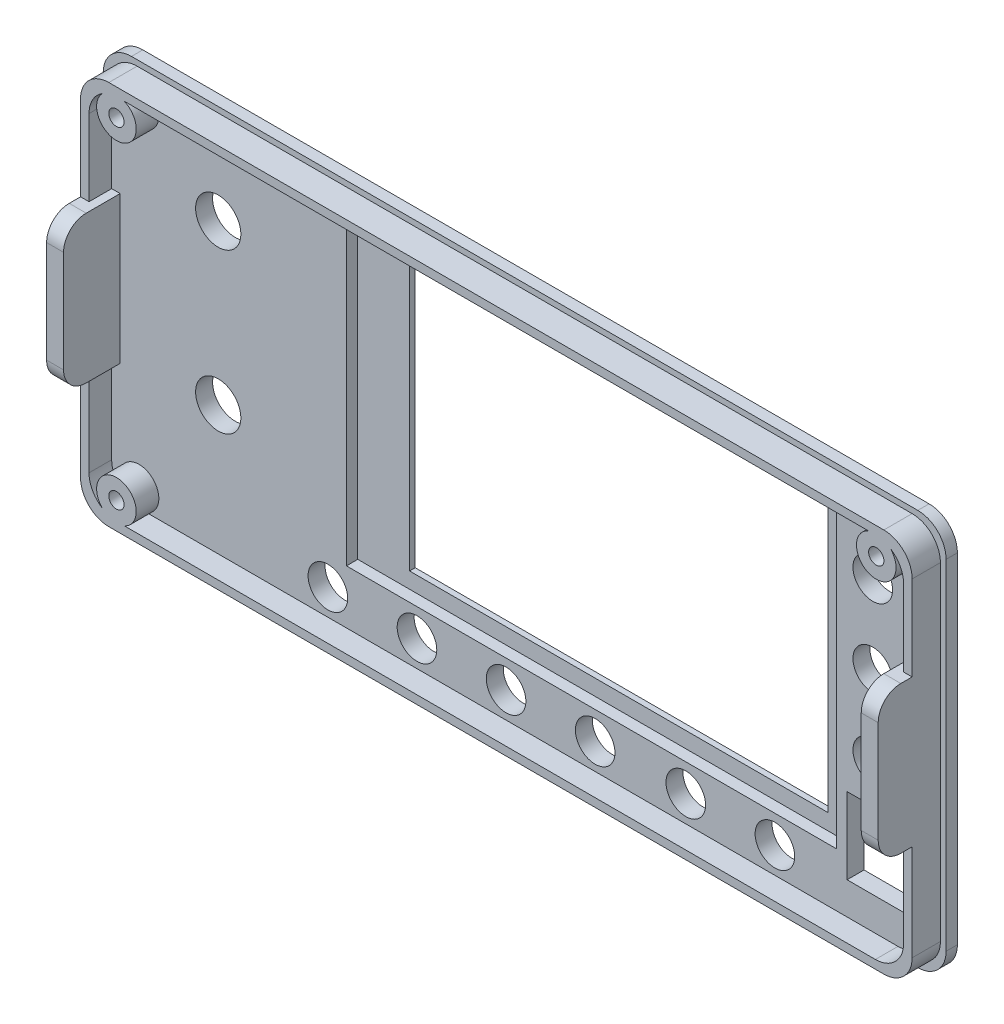
SolidWorks part; units mm, degrees
material "ПК/АБС"
ref_plane "Спереди" through (0, 0, 0) normal (0, 0, 1) x (1, 0, 0)
ref_plane "Сверху" through (0, 0, 0) normal (0, 1, 0) x (1, 0, 0)
ref_plane "Справа" through (0, 0, 0) normal (1, 0, 0) x (0, 0, -1)
sketch "Эскиз1" plane through (0, 0, 0) normal (0, 0, 1) x (1, 0, 0)
  line L1 (74.5, -35) -> (-74.5, -35)
  line L2 (74.5, -35) -> (74.5, 35)
  line L3 (74.5, 35) -> (-74.5, 35)
  line L4 (-74.5, -35) -> (-74.5, 35)
  line L5 (74.5, -35) -> (-74.5, 35) construction
  line L6 (74.5, 35) -> (-74.5, -35) construction
  point P0 (0, 0)
  dimension "D1" = 149
  dimension "D2" = 70
extrude "Бобышка-Вытянуть1" add sketch "Эскиз1" along normal blind 1
sketch "Эскиз2" plane through (0, 0, 1) normal (0, 0, 1) x (1, 0, 0)
  line L1 (73.5, -34) -> (-73.5, -34)
  line L2 (73.5, -34) -> (73.5, 34)
  line L3 (73.5, 34) -> (-73.5, 34)
  line L4 (-73.5, -34) -> (-73.5, 34)
  line L5 (73.5, -34) -> (-73.5, 34) construction
  line L6 (73.5, 34) -> (-73.5, -34) construction
  point P0 (0, 0)
  dimension "D1" = 147
  dimension "D2" = 68
extrude "Бобышка-Вытянуть2" add sketch "Эскиз2" along normal blind 2
fillet "Скругление1" radius 5 8 edges at (74.5, -35, 0.5) (73.5, -34, 2) (74.5, 35, 0.5) (73.5, 34, 2) (-74.5, -35, 0.5) (-73.5, -34, 2) (-74.5, 35, 0.5) (-73.5, 34, 2)
sketch "Эскиз3" plane through (0, 0, 3) normal (0, 0, 1) x (1, 0, 0)
  line L6 (-73.5, 29) -> (-73.5, -29) construction
  line L7 (-73.5, 14) -> (-70.5, 14)
  line L8 (-73.5, 14) -> (-73.5, -12)
  line L9 (-73.5, -12) -> (-70.5, -12)
  line L10 (-70.5, 14) -> (-70.5, -12)
  line L11 (73.5, 14) -> (70.5, 14)
  line L12 (73.5, 14) -> (73.5, -12)
  line L13 (73.5, -12) -> (70.5, -12)
  line L14 (70.5, 14) -> (70.5, -12)
  dimension "D1" = 3
extrude "Бобышка-Вытянуть3" add sketch "Эскиз3" along normal blind 10
fillet "Скругление2" radius 4 4 edges at (72, -12, 13) (72, 14, 13) (-72, -12, 13) (-72, 14, 13)
sketch "Эскиз6" plane through (0, 0, 3) normal (0, 0, 1) x (1, 0, 0)
  circle A0 centre (-67.16, 29.285) radius 3.5
  circle A1 centre (67.16, 29.285) radius 3.5
  circle A3 centre (-67.16, -29.285) radius 3.5
  point P0 (0, 0)
  dimension "D3" = 7
  dimension "D4" = 7
  dimension "D5" = 7
  dimension "D1" = 134.32
extrude "Бобышка-Вытянуть4" add sketch "Эскиз6" along normal blind 4
sketch "Эскиз7" plane through (0, 0, 3) normal (0, 0, 1) x (1, 0, 0)
  line L0 (68.5, 34) -> (-68.5, 34) construction
  line L1 (-30.5, 32.5) -> (56.16, 32.5)
  line L2 (-30.5, 32.5) -> (-30.5, -23)
  line L3 (-30.5, -23) -> (56.16, -23)
  line L4 (56.16, 32.5) -> (56.16, -23)
  line L5 (-73.5, 29) -> (-73.5, 14) construction
  line L6 (-68.5, -34) -> (68.5, -34) construction
  circle A0 centre (67.16, 29.285) radius 3.5 construction
  dimension "D1" = 43
  dimension "D2" = 11
  dimension "D3" = 11
  dimension "D4" = 1.5
extrude "Вырез-Вытянуть3" cut sketch "Эскиз7" against normal blind 2
sketch "Эскиз8" plane through (0, 0, 1) normal (0, 0, 1) x (1, 0, 0)
  line L2 (56.16, -23) -> (56.16, 32.5) construction
  line L5 (-30.5, -23) -> (56.16, -23) construction
  line L7 (-21.34, 28.8) -> (52.66, 28.8)
  line L8 (-21.34, 28.8) -> (-21.34, -20.2)
  line L9 (-21.34, -20.2) -> (52.66, -20.2)
  line L10 (52.66, 28.8) -> (52.66, -20.2)
  dimension "D1" = 74
  dimension "D2" = 49
  dimension "D3" = 3.5
  dimension "D4" = 2.8
extrude "Вырез-Вытянуть4" cut sketch "Эскиз8" against normal through all
sketch "Эскиз9" plane through (0, 0, 3) normal (0, 0, 1) x (1, 0, 0)
  circle A1 centre (62.54, -6.405) radius 3.5
  circle A2 centre (62.54, 21.595) radius 3.5
  circle A3 centre (62.54, 7.595) radius 3.5
  circle A4 centre (67.16, 29.285) radius 3.5 construction
  circle A5 centre (67.16, 29.285) radius 3.5 construction
  dimension "D6" = 7
  dimension "D1" = 7
  dimension "D2" = 7
  dimension "D3" = 4.62
  dimension "D4" = 7.69
  dimension "D5" = 14
  dimension "D7" = 14
sketch "Эскиз11" plane through (0, 0, 3) normal (0, 0, 1) x (1, 0, 0)
  circle A0 centre (-53.163, 18.448) radius 4
  circle A1 centre (-67.16, 29.285) radius 3.5 construction
  circle A2 centre (-53.163, -9.69) radius 4
  dimension "D1" = 13.997
  dimension "D2" = 10.837
  dimension "D3" = 8
  dimension "D4" = 8
  dimension "D5" = 28.138
extrude "Вырез-Вытянуть7" cut sketch "Эскиз11" against normal through all
sketch "Эскиз12" plane through (0, 0, 7) normal (0, 0, 1) x (1, 0, 0)
  circle A0 centre (-67.16, 29.285) radius 1.35
  dimension "D1" = 2.7
extrude "Вырез-Вытянуть8" cut sketch "Эскиз12" against normal blind 4
sketch "Эскиз13" plane through (0, 0, 7) normal (0, 0, 1) x (1, 0, 0)
  circle A0 centre (67.16, 29.285) radius 1.35
  dimension "D1" = 2.7
extrude "Вырез-Вытянуть9" cut sketch "Эскиз13" against normal blind 4
sketch "Эскиз14" plane through (0, 0, 7) normal (0, 0, 1) x (1, 0, 0)
  circle A0 centre (-67.16, -29.285) radius 1.35
  dimension "D1" = 2.7
extrude "Вырез-Вытянуть10" cut sketch "Эскиз14" against normal blind 4
sketch "Эскиз15" plane through (0, 0, 3) normal (0, 0, 1) x (1, 0, 0)
  line L1 (58, -13.3) -> (72, -13.3)
  line L2 (58, -13.3) -> (58, -26.8)
  line L3 (58, -26.8) -> (72, -26.8)
  line L4 (72, -13.3) -> (72, -26.8)
  line L9 (73.5, -29) -> (73.5, -12) construction
  line L10 (-68.5, -34) -> (68.5, -34) construction
  dimension "D1" = 14
  dimension "D2" = 1.5
  dimension "D3" = 13.5
  dimension "D4" = 7.2
extrude "Вырез-Вытянуть11" cut sketch "Эскиз15" against normal through all
extrude "Вырез-Вытянуть12" cut sketch "Эскиз9" against normal through all
sketch "Эскиз16" plane through (0, 0, 3) normal (0, 0, 1) x (1, 0, 0)
  circle A0 centre (45.24, -27.88) radius 3.5
  circle A1 centre (62.54, -6.405) radius 3.5 construction
  circle A2 centre (29.49, -27.88) radius 3.5
  circle A3 centre (13.47, -27.88) radius 3.5
  circle A4 centre (-2.28, -27.88) radius 3.5
  circle A5 centre (-18.03, -27.88) radius 3.5
  circle A6 centre (-33.78, -27.88) radius 3.5
  dimension "D1" = 17.3
  dimension "D2" = 21.475
  dimension "D3" = 7
  dimension "D4" = 7
  dimension "D5" = 7
  dimension "D6" = 7
  dimension "D7" = 15.75
  dimension "D9" = 15.75
  dimension "D10" = 7
  dimension "D11" = 7
  dimension "D12" = 15.75
  dimension "D13" = 15.75
extrude "Вырез-Вытянуть13" cut sketch "Эскиз16" against normal through all
sketch "Эскиз17" plane through (0, 0, 3) normal (0, 0, 1) x (1, 0, 0)
  line L0 (68.5, 34) -> (-68.5, 34) construction
  line L1 (67, -32.5) -> (-67, -32.5)
  line L2 (72, -27.5) -> (72, 27.5)
  line L3 (67, 32.5) -> (-67, 32.5)
  line L4 (-72, -27.5) -> (-72, 27.5)
  line L5 (72, -32.5) -> (-72, 32.5) construction
  line L6 (72, 32.5) -> (-72, -32.5) construction
  line L7 (-73.5, 29) -> (-73.5, -29) construction
  line L8 (-73.5, 29) -> (-73.5, 14) construction
  line L9 (68.5, -34) -> (-68.5, -34)
  line L10 (73.5, -29) -> (73.5, 29)
  line L11 (68.5, 34) -> (-68.5, 34)
  line L12 (-73.5, -29) -> (-73.5, 29)
  line L13 (73.5, -34) -> (-73.5, 34) construction
  line L14 (73.5, 34) -> (-73.5, -34) construction
  arc A0 (72, 27.5) -> (67, 32.5) centre (67, 27.5) ccw
  arc A1 (72, -27.5) -> (67, -32.5) centre (67, -27.5) cw
  arc A2 (-72, -27.5) -> (-67, -32.5) centre (-67, -27.5) ccw
  arc A3 (-72, 27.5) -> (-67, 32.5) centre (-67, 27.5) cw
  arc A4 (73.5, 29) -> (68.5, 34) centre (68.5, 29) ccw
  arc A5 (68.5, -34) -> (73.5, -29) centre (68.5, -29) ccw
  arc A6 (-73.5, -29) -> (-68.5, -34) centre (-68.5, -29) ccw
  arc A7 (-73.5, 29) -> (-68.5, 34) centre (-68.5, 29) cw
  point P0 (0, 0)
  point P22 (0, 0)
  dimension "D3" = 5
  dimension "D5" = 5
  dimension "D1" = 1.5
  dimension "D2" = 1.5
  dimension "D4" = 0
extrude "Бобышка-Вытянуть5" add sketch "Эскиз17" along normal blind 4
sketch "Эскиз18" plane through (0, 0, 1) normal (0, 0, 1) x (1, 0, 0)
  line L1 (69.5, -35) -> (-69.5, -35)
  line L2 (74.5, -30) -> (74.5, 30)
  line L3 (69.5, 35) -> (-69.5, 35)
  line L4 (-74.5, -30) -> (-74.5, 30)
  line L5 (74.5, -35) -> (-74.5, 35) construction
  line L6 (74.5, 35) -> (-74.5, -35) construction
  line L7 (68.5, -34) -> (-68.5, -34)
  line L8 (73.5, -29) -> (73.5, 29)
  line L9 (68.5, 34) -> (-68.5, 34)
  line L10 (-73.5, -29) -> (-73.5, 29)
  line L11 (73.5, -34) -> (-73.5, 34) construction
  line L12 (73.5, 34) -> (-73.5, -34) construction
  arc A0 (74.5, 30) -> (69.5, 35) centre (69.5, 30) ccw
  arc A1 (74.5, -30) -> (69.5, -35) centre (69.5, -30) cw
  arc A2 (-74.5, -30) -> (-69.5, -35) centre (-69.5, -30) ccw
  arc A3 (-74.5, 30) -> (-69.5, 35) centre (-69.5, 30) cw
  arc A4 (-73.5, -29) -> (-68.5, -34) centre (-68.5, -29) ccw
  arc A5 (73.5, -29) -> (68.5, -34) centre (68.5, -29) cw
  arc A6 (73.5, 29) -> (68.5, 34) centre (68.5, 29) ccw
  arc A7 (-73.5, 29) -> (-68.5, 34) centre (-68.5, 29) cw
  point P0 (0, 0)
  point P18 (0, 0)
  dimension "D1" = 5
  dimension "D2" = 5
extrude "Бобышка-Вытянуть6" add sketch "Эскиз18" along normal blind 1
